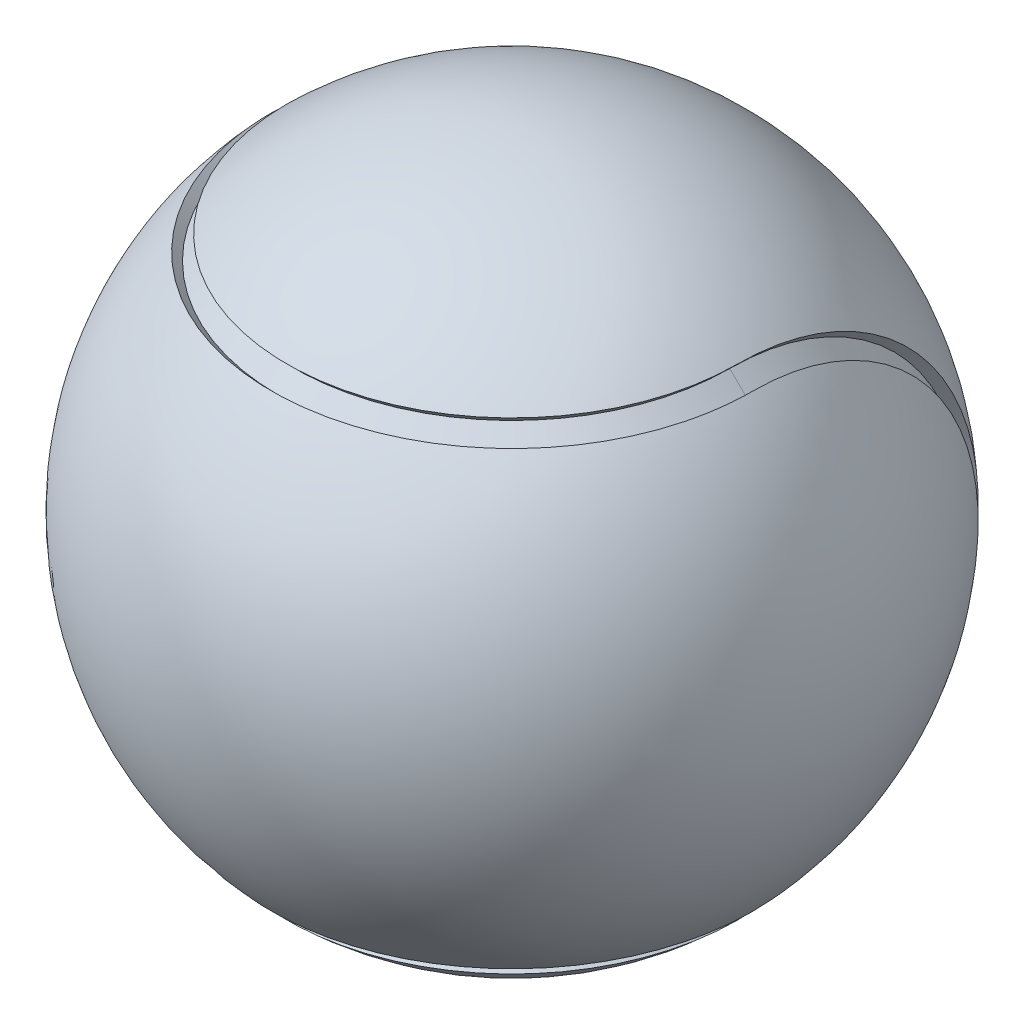
SolidWorks part; units mm, degrees
ref_plane "Front Plane" through (0, 0, 0) normal (0, 0, 1) x (1, 0, 0)
ref_plane "Top Plane" through (0, 0, 0) normal (0, 1, 0) x (1, 0, 0)
ref_plane "Right Plane" through (0, 0, 0) normal (1, 0, 0) x (0, 0, -1)
sketch "Sketch8" plane through (0, 0, 0) normal (0, 0, 1) x (1, 0, 0)
  line L0 (-38.1, 0) -> (38.1, 0)
  arc A0 (-38.1, 0) -> (38.1, 0) centre (0, 0) cw
  point P2 (0, 0)
  dimension "D1" = 76.2
revolve "Revolve2" add sketch "Sketch8" angle 360 about L0
sketch "Sketch9" plane through (0, 0, 0) normal (0, 0, 1) x (1, 0, 0)
  line L1 (26.9408, -26.9408) -> (-26.9408, -26.9408) construction
  line L2 (26.9408, -26.9408) -> (26.9408, 26.9408) construction
  line L3 (26.9408, 26.9408) -> (-26.9408, 26.9408)
  line L4 (-26.9408, -26.9408) -> (-26.9408, 26.9408) construction
  line L5 (26.9408, -26.9408) -> (-26.9408, 26.9408) construction
  line L6 (26.9408, 26.9408) -> (-26.9408, -26.9408) construction
  circle A0 centre (0, 0) radius 38.1 construction
  point P0 (0, 0)
curve "Curve6"
sketch "Sketch10" plane through (0, 0, 0) normal (0, 0, 1) x (1, 0, 0)
  line L0 (26.9408, -26.9408) -> (26.9408, 26.9408) construction
  line L1 (26.9408, -26.9408) -> (26.9408, 26.9408)
curve "Curve7"
sketch "Sketch11" plane through (0, 0, 0) normal (0, 0, 1) x (1, 0, 0)
  line L0 (26.9408, -26.9408) -> (-26.9408, -26.9408) construction
  line L1 (26.9408, -26.9408) -> (-26.9408, -26.9408)
curve "Curve8"
sketch "Sketch12" plane through (0, 0, 0) normal (0, 0, 1) x (1, 0, 0)
  line L0 (-26.9408, -26.9408) -> (-26.9408, 26.9408) construction
  line L1 (-26.9408, -26.9408) -> (-26.9408, 26.9408)
curve "Curve9"
sketch "Sketch13" plane through (0, 0, 0) normal (0, 0, 1) x (1, 0, 0)
  line L1 (-26.9408, 28.7368) -> (-28.7368, 26.9408)
  line L2 (-26.9408, 28.7368) -> (-25.1447, 26.9408)
  line L3 (-25.1447, 26.9408) -> (-26.9408, 25.1447)
  line L4 (-28.7368, 26.9408) -> (-26.9408, 25.1447)
  line L5 (-26.9408, 28.7368) -> (-26.9408, 25.1447) construction
  line L6 (-25.1447, 26.9408) -> (-28.7368, 26.9408) construction
  line L8 (26.9408, -26.9408) -> (-26.9408, 26.9408) construction
  point P0 (-26.9408, 26.9408)
  dimension "D1" = 2.54
curve "CompCurve1"
sweep "Cut-Sweep2" cut profiles "Sketch13" path "CompCurve1"
